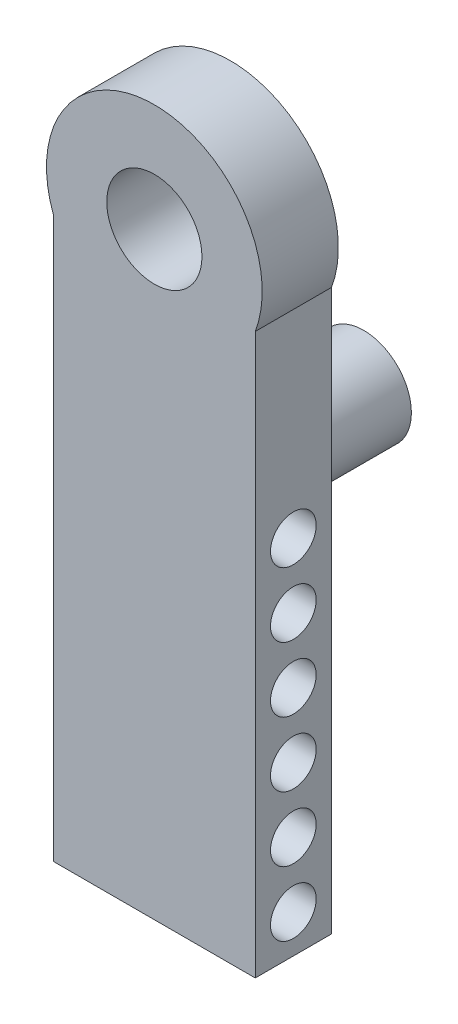
SolidWorks part; units mm, degrees
ref_plane "Front Plane" through (0, 0, 0) normal (0, 0, 1) x (1, 0, 0)
ref_plane "Top Plane" through (0, 0, 0) normal (0, 1, 0) x (1, 0, 0)
ref_plane "Right Plane" through (0, 0, 0) normal (1, 0, 0) x (0, 0, -1)
sketch "Sketch2" plane through (0, 0, 0) normal (0, 0, 1) x (1, 0, 0)
  line L0 (-64.427, -74.4159) -> (-90.927, -74.4159) construction
  line L1 (-90.927, -74.4159) -> (-37.927, -74.4159) construction
  line L2 (-37.927, -74.4159) -> (-37.927, -221.4559)
  line L3 (-90.927, -74.4159) -> (-90.927, -221.4559)
  line L4 (-90.927, -221.4559) -> (-37.927, -221.4559)
  circle A1 centre (-64.427, -64.4159) radius 10
  arc A2 (-37.927, -74.4159) -> (-90.927, -74.4159) centre (-64.427, -64.4159) ccw
  dimension "D1" = 53
  dimension "D2" = 20
extrude "Boss-Extrude2" add sketch "Sketch2" along normal blind 20 contours L2 A2 L3 L4 A1
sketch "Sketch6" plane through (-90.927, 0, 0) normal (-1, 0, 0) x (0, 0, 1)
  line L0 (20, -221.4559) -> (0, -221.4559) construction
  circle A0 centre (10, -211.4559) radius 6
  dimension "D1" = 12
  dimension "D2" = 10
sketch "Sketch8" plane through (-90.927, 0, 0) normal (-1, 0, 0) x (0, 0, 1)
  circle A0 centre (10, -194.4559) radius 6
  circle A1 centre (10, -177.4559) radius 6
  circle A2 centre (10, -160.4559) radius 6
  circle A3 centre (10, -143.4559) radius 6
  circle A4 centre (10, -126.4559) radius 6
  circle A6 centre (10, -211.4559) radius 6 construction
  dimension "D2" = 12
  dimension "D3" = 12
  dimension "D4" = 12
  dimension "D5" = 12
  dimension "D6" = 12
  dimension "D7" = 17
  dimension "D8" = 17
  dimension "D9" = 17
  dimension "D10" = 17
  dimension "D11" = 17
extrude "Cut-Extrude1" cut sketch "Sketch8" against normal through all
extrude "Cut-Extrude2" cut sketch "Sketch6" against normal through all contours A0
sketch "Sketch9" plane through (0, 0, 20) normal (0, 0, 1) x (1, 0, 0)
  circle A0 centre (-64.427, -64.4159) radius 12.5
  dimension "D1" = 25
extrude "Cut-Extrude3" cut sketch "Sketch9" against normal blind 23
sketch "Sketch11" plane through (0, 0, 0) normal (0, 0, 1) x (1, 0, 0)
  line L0 (-64.427, -64.4159) -> (-64.427, -127.4159)
  circle A0 centre (-64.427, -64.4159) radius 12.5
  circle A1 centre (-64.427, -127.4159) radius 12.5
  dimension "D2" = 25
  dimension "D1" = 63
extrude "Boss-Extrude4" add sketch "Sketch11" against normal blind 35
